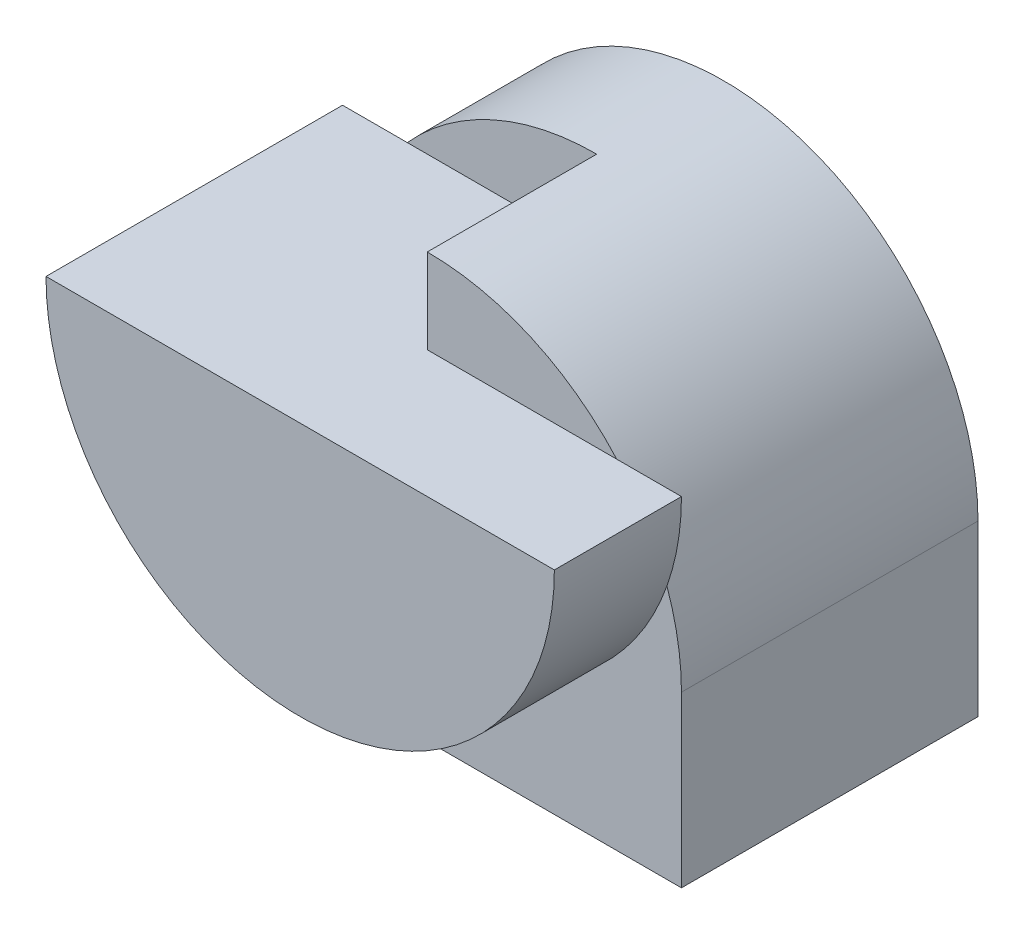
SolidWorks part; units mm, degrees
ref_plane "Front Plane" through (0, 0, 0) normal (0, 0, 1) x (1, 0, 0)
ref_plane "Top Plane" through (0, 0, 0) normal (0, 1, 0) x (1, 0, 0)
ref_plane "Right Plane" through (0, 0, 0) normal (1, 0, 0) x (0, 0, -1)
sketch "Sketch11" plane through (0, 0, 0) normal (0, 0, 1) x (1, 0, 0)
  line L0 (3, 0) -> (3, -2)
  line L1 (3, -2) -> (-3, -2)
  line L2 (-3, -2) -> (-3, 0)
  arc A0 (-3, 0) -> (3, 0) centre (0, 0) cw
  dimension "D1" = 3
  dimension "D2" = 2
  dimension "D3" = 6
extrude "Boss-Extrude7" add sketch "Sketch11" along normal blind 3.5
sketch "Sketch12" plane through (0, -2, 0) normal (0, -1, 0) x (-1, 0, 0)
  line L0 (3, -3.5) -> (3, 0) construction
  line L1 (3, -1.5) -> (0, -1.5)
  line L2 (3, -1.5) -> (3, -3.5)
  line L3 (3, -3.5) -> (0, -3.5)
  line L4 (0, -1.5) -> (0, -3.5)
  line L5 (-3, -3.5) -> (3, -3.5) construction
  dimension "D1" = 2
extrude "Cut-Extrude5" cut sketch "Sketch12" against normal blind 5.5
sketch "Sketch13" plane through (0, 0, 3.5) normal (0, 0, 1) x (1, 0, 0)
  line L0 (0, 3) -> (0, -2) construction
  line L1 (-3, 2) -> (3, 2)
  arc A0 (3, 2) -> (-3, 2) centre (0, 2) cw
  dimension "D1" = 3
  dimension "D2" = 1
  dimension "D3" = 6
extrude "Boss-Extrude8" add sketch "Sketch13" along normal blind 1.5 and the other way blind 2
sketch "Sketch14" plane through (0, 0, 1.5) normal (0, 0, -1) x (-1, 0, 0)
  line L0 (-3, 2) -> (-2.2361, 2)
  arc A0 (-3, 2) -> (-2.8284, 1) centre (0, 2) ccw
  arc A1 (3, 0) -> (-3, 0) centre (0, 0) ccw construction
  arc A2 (-2.2361, 2) -> (-2.8284, 1) centre (0, 0) ccw
  arc M1 (-2.8284, 1) -> (-2.2361, 2) centre (0, 0) cw
  line M2 (-2.2361, 2) -> (-3, 2)
  arc M3 (-3, 2) -> (-2.8284, 1) centre (0, 2) ccw
extrude "Cut-Extrude6" cut sketch "Sketch14" against normal blind 2 contours M3 M1 M2
